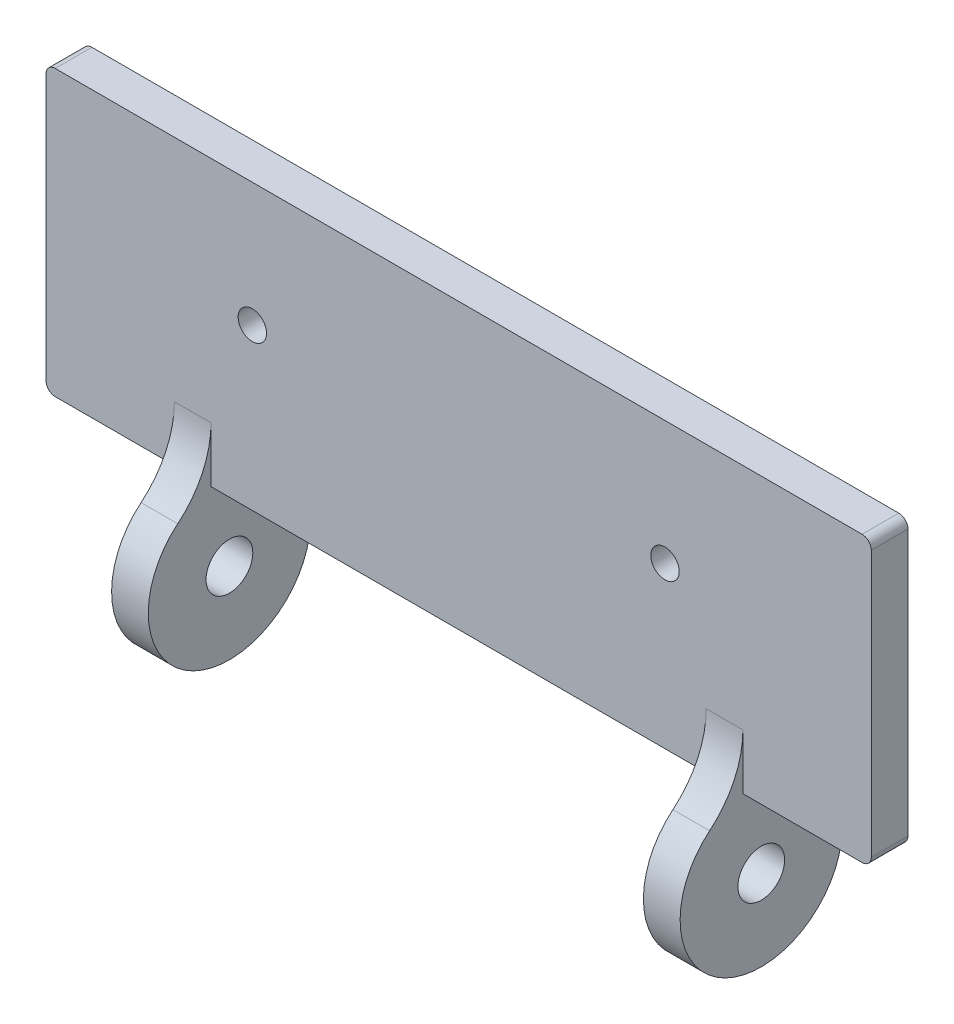
SolidWorks part; units mm, degrees
ref_plane "Ebene vorne" through (0, 0, 0) normal (0, 0, 1) x (1, 0, 0)
ref_plane "Ebene oben" through (0, 0, 0) normal (0, 1, 0) x (1, 0, 0)
ref_plane "Ebene rechts" through (0, 0, 0) normal (1, 0, 0) x (0, 0, -1)
sketch "Skizze1" plane through (0, 0, 0) normal (0, 0, 1) x (1, 0, 0)
  line L0 (-35.0685, 23.8011) -> (-35.0685, -30.8934) construction
  line L1 (40.9315, 21.491) -> (-49.0685, 21.491)
  line L2 (40.9315, 21.491) -> (40.9315, -9.509)
  line L3 (40.9315, -9.509) -> (-49.0685, -9.509)
  line L4 (-49.0685, 21.491) -> (-49.0685, -9.509)
  line L5 (26.9315, 23.8011) -> (26.9315, -30.8934) construction
  dimension "D1" = 62
  dimension "D2" = 31
  dimension "D3" = 90
  dimension "D4" = 14
  dimension "D5" = 14
extrude "Aufsatz-Linear austragen1" add sketch "Skizze1" along normal blind 4
ref_plane "Ebene1" through (26.9315, 0, 0) normal (1, 0, 0) x (0, 0, -1)
sketch "Skizze4" plane through (26.9315, 0, 0) normal (1, 0, 0) x (0, 0, -1)
  line L0 (-2, 26.2502) -> (-2, -25.4065) construction
  line L1 (-10.8872, -6.509) -> (10.6288, -6.509) construction
  line L4 (0, -9.509) -> (0, 21.491)
  line L5 (0, 21.491) -> (-4, 21.491)
  line L6 (-4, 21.491) -> (-4, -9.509)
  line L7 (-4, -9.509) -> (0, -9.509)
  line L8 (0, -9.509) -> (0, 21.491) construction
  line L9 (0, 21.491) -> (-4, 21.491) construction
  line L10 (-4, 21.491) -> (-4, -9.509) construction
  line L11 (-4, -9.509) -> (0, -9.509) construction
  circle A1 centre (-2, -18.0199) radius 8.85
  circle A2 centre (-2, -18.0199) radius 2.55
  circle A3 centre (-2, -18.0199) radius 8.5 construction
  point P8 (-2, -18.3002)
  point P11 (-2, -17.888)
  point P13 (-2, -18.0199)
  dimension "D4" = 17.7
  dimension "D5" = 5.1
  dimension "D6" = 17
  dimension "D2" = 2
  dimension "D3" = 3
  dimension "D1" = 0
extrude "Aufsatz-Linear austragen3" add sketch "Skizze4" against normal blind 4
pattern_linear "Lineares Muster1" count 2 spacing 58 along (-1, 0, 0) of "Aufsatz-Linear austragen3"
fillet "Verrundung2" radius 10 2 edges at (24.9315, -9.3989, 4) (-33.0685, -9.3989, 4)
fillet "Verrundung3" radius 2 2 edges at (-33.0685, -9.3989, 0) (24.9315, -9.3989, 0)
sketch "Skizze6" plane through (0, 0, 4) normal (0, 0, 1) x (1, 0, 0)
  line L0 (-55.2894, 7.991) -> (56.5947, 7.991) construction
  line L1 (-4.0685, 25.7666) -> (-4.0685, -17.0468) construction
  line L2 (40.9315, -9.509) -> (40.9315, 21.491) construction
  line L3 (40.9315, 21.491) -> (-49.0685, 21.491) construction
  line L4 (-49.0685, 21.491) -> (-49.0685, -9.509) construction
  circle A0 centre (-26.5685, 7.991) radius 1.55
  circle A1 centre (18.4315, 7.991) radius 1.55
  dimension "D3" = 3.1
  dimension "D4" = 3.1
  dimension "D1" = 45
  dimension "D2" = 13.5
  dimension "D5" = 45
  dimension "D6" = 22.5
  dimension "D7" = 22.5
extrude "Schnitt-Linear austragen1" cut sketch "Skizze6" against normal blind 4
fillet "Verrundung4" radius 1 4 edges at (-49.0685, -9.509, 2) (-49.0685, 21.491, 2) (40.9315, -9.509, 2) (40.9315, 21.491, 2)
